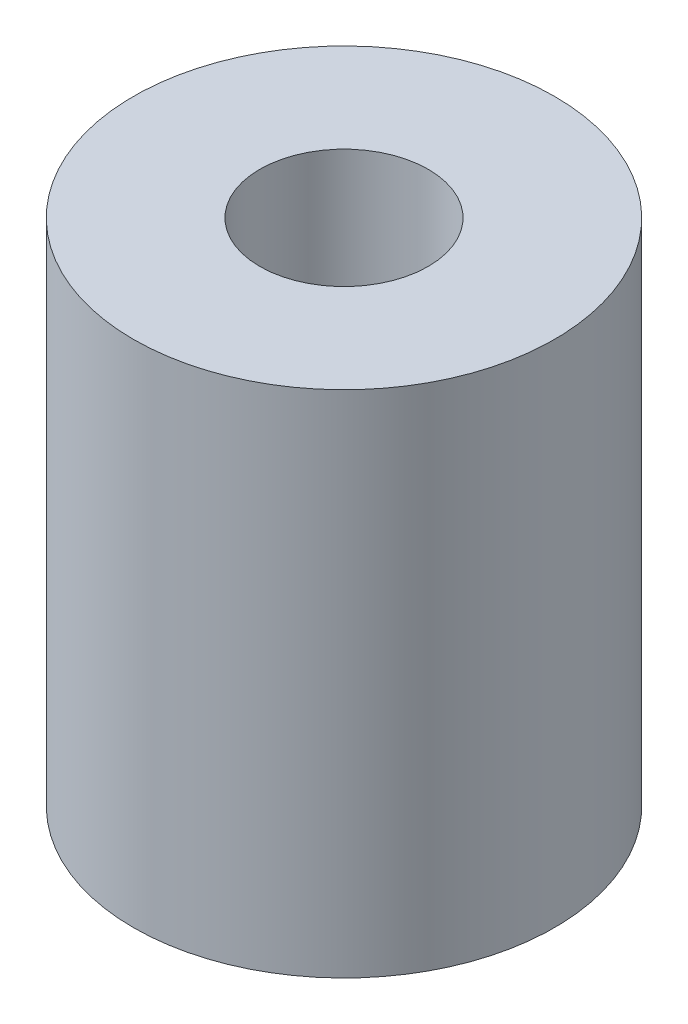
SolidWorks part; units mm, degrees
ref_plane "Front" through (0, 0, 0) normal (0, 0, 1) x (1, 0, 0)
ref_plane "Top" through (0, 0, 0) normal (0, 1, 0) x (1, 0, 0)
ref_plane "Right" through (0, 0, 0) normal (1, 0, 0) x (0, 0, -1)
sketch "Sketch1" plane through (0, 0, 0) normal (0, 1, 0) x (1, 0, 0)
  circle A0 centre (0, 0) radius 2
  circle A1 centre (0, 0) radius 5
  dimension "D1" = 4
  dimension "D2" = 3
extrude "Boss-Extrude1" add sketch "Sketch1" along normal mid plane 12.1
